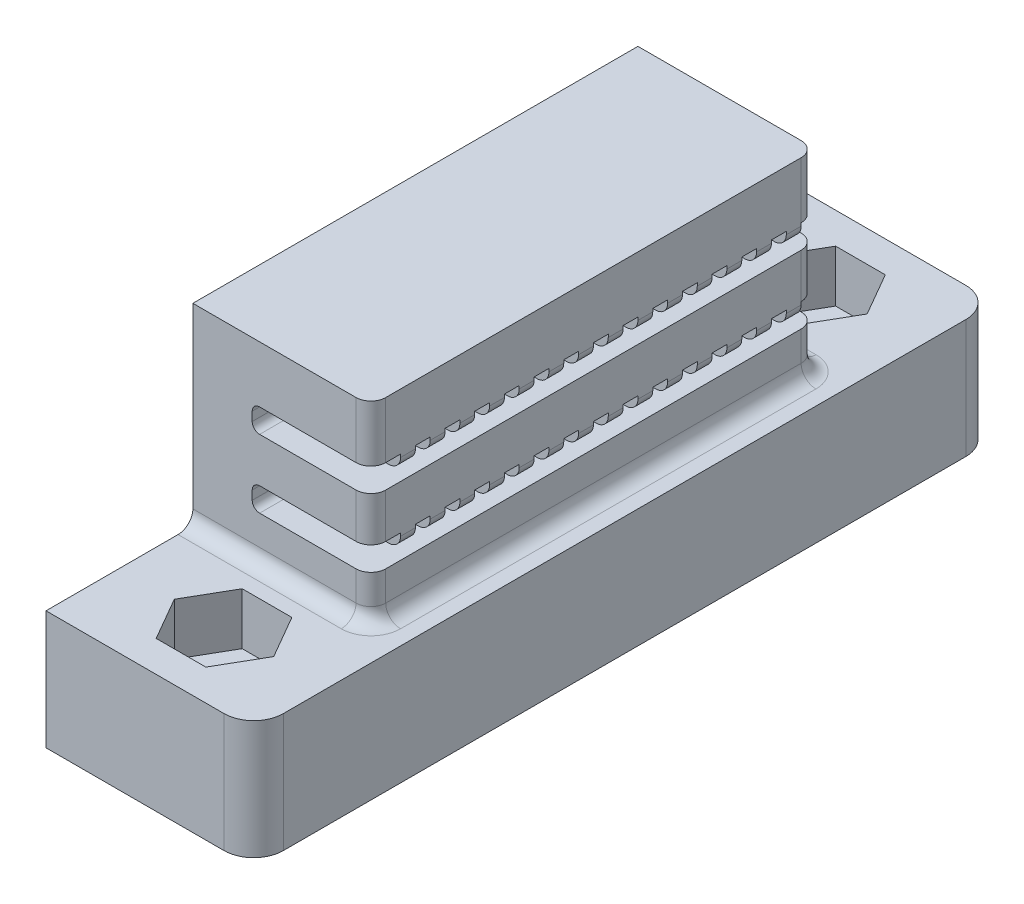
SolidWorks part; units mm, degrees
ref_plane "Alzado" through (0, 0, 0) normal (0, 0, 1) x (1, 0, 0)
ref_plane "Planta" through (0, 0, 0) normal (0, 1, 0) x (1, 0, 0)
ref_plane "Vista lateral" through (0, 0, 0) normal (1, 0, 0) x (0, 0, -1)
sketch "Croquis1" plane through (0, 0, 0) normal (0, 1, 0) x (1, 0, 0)
  line L0 (0, 25) -> (14, 25) construction
  line L1 (0, 0) -> (14, 0)
  line L2 (0, 0) -> (0, 50)
  line L3 (0, 50) -> (14, 50)
  line L4 (14, 0) -> (14, 50)
  line L5 (7, 50) -> (7, 0) construction
  circle A0 centre (7, 45) radius 1.55
  circle A1 centre (7, 5) radius 1.55
  dimension "D3" = 3.1
  dimension "D1" = 50
  dimension "D2" = 14
  dimension "D4" = 20
extrude "Saliente-Extruir1" add sketch "Croquis1" along normal blind 8
sketch "Croquis2" plane through (0, 8, 0) normal (0, 1, 0) x (1, 0, 0)
  line L1 (10.3486, 45) -> (8.6743, 47.9)
  line L2 (8.6743, 47.9) -> (5.3257, 47.9)
  line L3 (5.3257, 47.9) -> (3.6514, 45)
  line L4 (3.6514, 45) -> (5.3257, 42.1)
  line L5 (5.3257, 42.1) -> (8.6743, 42.1)
  line L6 (8.6743, 42.1) -> (10.3486, 45)
  line L7 (10.3486, 5) -> (8.6743, 7.9)
  line L8 (8.6743, 7.9) -> (5.3257, 7.9)
  line L9 (5.3257, 7.9) -> (3.6514, 5)
  line L10 (3.6514, 5) -> (5.3257, 2.1)
  line L11 (5.3257, 2.1) -> (8.6743, 2.1)
  line L12 (8.6743, 2.1) -> (10.3486, 5)
  circle A2 centre (7, 45) radius 2.9 construction
  circle A3 centre (7, 5) radius 2.9 construction
  dimension "D1" = 5.8
  dimension "D2" = 5.8
extrude "Cortar-Extruir1" cut sketch "Croquis2" against normal blind 3.5
sketch "Croquis3" plane through (0, 8, 0) normal (0, 1, 0) x (1, 0, 0)
  line L0 (0, 50) -> (0, 0) construction
  line L1 (0, 39.9) -> (14, 39.9)
  line L2 (0, 39.9) -> (0, 9.9)
  line L3 (0, 9.9) -> (14, 9.9)
  line L4 (14, 39.9) -> (14, 9.9)
  line L5 (14, 0) -> (14, 50) construction
  line L6 (5.3257, 42.1) -> (8.6743, 42.1) construction
  dimension "D1" = 30
  dimension "D2" = 2.2
extrude "Saliente-Extruir3" add sketch "Croquis3" along normal blind 13
sketch "Croquis4" plane through (14, 0, 0) normal (1, 0, 0) x (0, 0, -1)
  line L0 (39.9, 21) -> (39.9, 8) construction
  line L1 (39.9, 17.2) -> (38.9, 17.2)
  line L2 (39.9, 17.2) -> (39.9, 15.6)
  line L3 (39.9, 15.6) -> (9.9, 15.6)
  line L4 (9.9, 17.2) -> (9.9, 15.6)
  line L5 (9.9, 21) -> (9.9, 8) construction
  line L6 (39.9, 8) -> (50, 8) construction
  line L7 (39.9, 12.6) -> (38.9, 12.6)
  line L8 (39.9, 12.6) -> (39.9, 11)
  line L9 (39.9, 11) -> (9.9, 11)
  line L10 (9.9, 12.6) -> (9.9, 11)
  line L11 (36.9, 17.2) -> (36.9, 16.2)
  line L13 (38.9, 17.2) -> (38.9, 16.2)
  line L14 (38.9, 16.2) -> (37.9, 16.2)
  line L15 (37.9, 17.2) -> (37.9, 16.2)
  line L16 (36.9, 16.2) -> (35.9, 16.2)
  line L17 (35.9, 17.2) -> (35.9, 16.2)
  line L18 (34.9, 17.2) -> (34.9, 16.2)
  line L19 (34.9, 16.2) -> (33.9, 16.2)
  line L20 (33.9, 17.2) -> (33.9, 16.2)
  line L21 (32.9, 17.2) -> (32.9, 16.2)
  line L22 (32.9, 16.2) -> (31.9, 16.2)
  line L23 (31.9, 17.2) -> (31.9, 16.2)
  line L24 (30.9, 17.2) -> (30.9, 16.2)
  line L25 (30.9, 16.2) -> (29.9, 16.2)
  line L26 (29.9, 17.2) -> (29.9, 16.2)
  line L27 (28.9, 17.2) -> (28.9, 16.2)
  line L28 (28.9, 16.2) -> (27.9, 16.2)
  line L29 (27.9, 17.2) -> (27.9, 16.2)
  line L30 (26.9, 17.2) -> (26.9, 16.2)
  line L31 (26.9, 16.2) -> (25.9, 16.2)
  line L32 (25.9, 17.2) -> (25.9, 16.2)
  line L33 (24.9, 17.2) -> (24.9, 16.2)
  line L34 (24.9, 16.2) -> (23.9, 16.2)
  line L35 (23.9, 17.2) -> (23.9, 16.2)
  line L36 (22.9, 17.2) -> (22.9, 16.2)
  line L37 (22.9, 16.2) -> (21.9, 16.2)
  line L38 (21.9, 17.2) -> (21.9, 16.2)
  line L39 (20.9, 17.2) -> (20.9, 16.2)
  line L40 (20.9, 16.2) -> (19.9, 16.2)
  line L41 (19.9, 17.2) -> (19.9, 16.2)
  line L42 (18.9, 17.2) -> (18.9, 16.2)
  line L43 (18.9, 16.2) -> (17.9, 16.2)
  line L44 (17.9, 17.2) -> (17.9, 16.2)
  line L45 (16.9, 17.2) -> (16.9, 16.2)
  line L46 (16.9, 16.2) -> (15.9, 16.2)
  line L47 (15.9, 17.2) -> (15.9, 16.2)
  line L48 (14.9, 17.2) -> (14.9, 16.2)
  line L49 (14.9, 16.2) -> (13.9, 16.2)
  line L50 (13.9, 17.2) -> (13.9, 16.2)
  line L51 (12.9, 17.2) -> (12.9, 16.2)
  line L52 (12.9, 16.2) -> (11.9, 16.2)
  line L53 (11.9, 17.2) -> (11.9, 16.2)
  line L54 (38.9, 17.2) -> (36.9, 17.2) construction
  line L55 (36.9, 12.6) -> (36.9, 11.6)
  line L57 (38.9, 12.6) -> (38.9, 11.6)
  line L58 (38.9, 11.6) -> (37.9, 11.6)
  line L59 (37.9, 12.6) -> (37.9, 11.6)
  line L60 (36.9, 11.6) -> (35.9, 11.6)
  line L61 (35.9, 12.6) -> (35.9, 11.6)
  line L62 (34.9, 12.6) -> (34.9, 11.6)
  line L63 (34.9, 11.6) -> (33.9, 11.6)
  line L64 (33.9, 12.6) -> (33.9, 11.6)
  line L65 (32.9, 12.6) -> (32.9, 11.6)
  line L66 (32.9, 11.6) -> (31.9, 11.6)
  line L67 (31.9, 12.6) -> (31.9, 11.6)
  line L68 (30.9, 12.6) -> (30.9, 11.6)
  line L69 (30.9, 11.6) -> (29.9, 11.6)
  line L70 (29.9, 12.6) -> (29.9, 11.6)
  line L71 (28.9, 12.6) -> (28.9, 11.6)
  line L72 (28.9, 11.6) -> (27.9, 11.6)
  line L73 (27.9, 12.6) -> (27.9, 11.6)
  line L74 (26.9, 12.6) -> (26.9, 11.6)
  line L75 (26.9, 11.6) -> (25.9, 11.6)
  line L76 (25.9, 12.6) -> (25.9, 11.6)
  line L77 (24.9, 12.6) -> (24.9, 11.6)
  line L78 (24.9, 11.6) -> (23.9, 11.6)
  line L79 (23.9, 12.6) -> (23.9, 11.6)
  line L80 (22.9, 12.6) -> (22.9, 11.6)
  line L81 (22.9, 11.6) -> (21.9, 11.6)
  line L82 (21.9, 12.6) -> (21.9, 11.6)
  line L83 (20.9, 12.6) -> (20.9, 11.6)
  line L84 (20.9, 11.6) -> (19.9, 11.6)
  line L85 (19.9, 12.6) -> (19.9, 11.6)
  line L86 (18.9, 12.6) -> (18.9, 11.6)
  line L87 (18.9, 11.6) -> (17.9, 11.6)
  line L88 (17.9, 12.6) -> (17.9, 11.6)
  line L89 (16.9, 12.6) -> (16.9, 11.6)
  line L90 (16.9, 11.6) -> (15.9, 11.6)
  line L91 (15.9, 12.6) -> (15.9, 11.6)
  line L92 (14.9, 12.6) -> (14.9, 11.6)
  line L93 (14.9, 11.6) -> (13.9, 11.6)
  line L94 (13.9, 12.6) -> (13.9, 11.6)
  line L95 (12.9, 12.6) -> (12.9, 11.6)
  line L96 (12.9, 11.6) -> (11.9, 11.6)
  line L97 (11.9, 12.6) -> (11.9, 11.6)
  line L98 (38.9, 12.6) -> (36.9, 12.6) construction
  line L99 (37.9, 17.2) -> (36.9, 17.2)
  line L100 (35.9, 17.2) -> (34.9, 17.2)
  line L101 (33.9, 17.2) -> (32.9, 17.2)
  line L102 (31.9, 17.2) -> (30.9, 17.2)
  line L103 (29.9, 17.2) -> (28.9, 17.2)
  line L104 (27.9, 17.2) -> (26.9, 17.2)
  line L105 (25.9, 17.2) -> (24.9, 17.2)
  line L106 (23.9, 17.2) -> (22.9, 17.2)
  line L107 (21.9, 17.2) -> (20.9, 17.2)
  line L108 (19.9, 17.2) -> (18.9, 17.2)
  line L109 (17.9, 17.2) -> (16.9, 17.2)
  line L110 (15.9, 17.2) -> (14.9, 17.2)
  line L111 (13.9, 17.2) -> (12.9, 17.2)
  line L112 (11.9, 17.2) -> (9.9, 17.2)
  line L113 (37.9, 12.6) -> (36.9, 12.6)
  line L114 (35.9, 12.6) -> (34.9, 12.6)
  line L115 (33.9, 12.6) -> (32.9, 12.6)
  line L116 (31.9, 12.6) -> (30.9, 12.6)
  line L117 (29.9, 12.6) -> (28.9, 12.6)
  line L118 (27.9, 12.6) -> (26.9, 12.6)
  line L119 (25.9, 12.6) -> (24.9, 12.6)
  line L120 (23.9, 12.6) -> (22.9, 12.6)
  line L121 (21.9, 12.6) -> (20.9, 12.6)
  line L122 (19.9, 12.6) -> (18.9, 12.6)
  line L123 (17.9, 12.6) -> (16.9, 12.6)
  line L124 (15.9, 12.6) -> (14.9, 12.6)
  line L125 (13.9, 12.6) -> (12.9, 12.6)
  line L126 (11.9, 12.6) -> (9.9, 12.6)
  dimension "D1" = 1.6
  dimension "D2" = 1.6
  dimension "D3" = 3
  dimension "D4" = 3
  dimension "D5" = 1
  dimension "D6" = 1
  dimension "D7" = 1
  dimension "D9" = 2
  dimension "D10" = 1
  dimension "D11" = 1
  dimension "D12" = 1
  dimension "D14" = 2
  dimension "D8" = 14
  dimension "D13" = 14
extrude "Cortar-Extruir2" cut sketch "Croquis4" against normal blind 10
sketch "Croquis5" plane through (14, 0, 0) normal (1, 0, 0) x (0, 0, -1)
  line L1 (39.9, 8) -> (9.9, 8)
  line L2 (39.9, 8) -> (39.9, 21)
  line L3 (39.9, 21) -> (9.9, 21)
  line L4 (9.9, 8) -> (9.9, 21)
extrude "Cortar-Extruir3" cut sketch "Croquis5" against normal blind 2
fillet "Redondeo1" radius 0.8 28 edges at (12, 11.6, -12.4) (12, 11.6, -14.4) (12, 11.6, -16.4) (12, 11.6, -18.4) (12, 11.6, -20.4) (12, 11.6, -22.4) (12, 11.6, -24.4) (12, 11.6, -26.4) (12, 11.6, -28.4) (12, 11.6, -30.4) (12, 11.6, -32.4) (12, 11.6, -34.4) (12, 11.6, -36.4) (12, 11.6, -38.4) (12, 16.2, -38.4) (12, 16.2, -36.4) (12, 16.2, -34.4) (12, 16.2, -32.4) (12, 16.2, -30.4) (12, 16.2, -28.4) (12, 16.2, -26.4) (12, 16.2, -24.4) (12, 16.2, -22.4) (12, 16.2, -20.4) (12, 16.2, -18.4) (12, 16.2, -16.4) (12, 16.2, -14.4) (12, 16.2, -12.4)
fillet "Redondeo2" radius 2 2 edges at (14, 4, -50) (14, 4, 0)
fillet "Redondeo3" radius 1 6 edges at (12, 19.1, -39.9) (12, 14.1, -39.9) (12, 9.5, -39.9) (12, 9.5, -9.9) (12, 14.1, -9.9) (12, 19.1, -9.9)
fillet "Redondeo4" radius 1 5 edges at (5.5, 8, -9.9) (11.7071, 8, -10.1929) (12, 8, -24.9) (11.7071, 8, -39.6071) (5.5, 8, -39.9)
fillet "Redondeo5" radius 0.5 32 edges at (4, 12.6, -10.9) (4, 12.6, -13.4) (4, 12.6, -15.4) (4, 12.6, -17.4) (4, 12.6, -19.4) (4, 12.6, -21.4) (4, 12.6, -25.4) (4, 12.6, -23.4) (4, 12.6, -27.4) (4, 12.6, -29.4) (4, 12.6, -31.4) (4, 12.6, -33.4) (4, 12.6, -35.4) (4, 12.6, -37.4) (4, 12.6, -39.4) (4, 17.2, -39.4) (4, 17.2, -37.4) (4, 17.2, -35.4) (4, 17.2, -33.4) (4, 17.2, -31.4) (4, 17.2, -29.4) (4, 17.2, -27.4) (4, 17.2, -25.4) (4, 17.2, -23.4) (4, 17.2, -21.4) (4, 17.2, -19.4) (4, 17.2, -17.4) (4, 17.2, -15.4) (4, 17.2, -13.4) (4, 17.2, -10.9) (4, 15.6, -24.9) (4, 11, -24.9)
